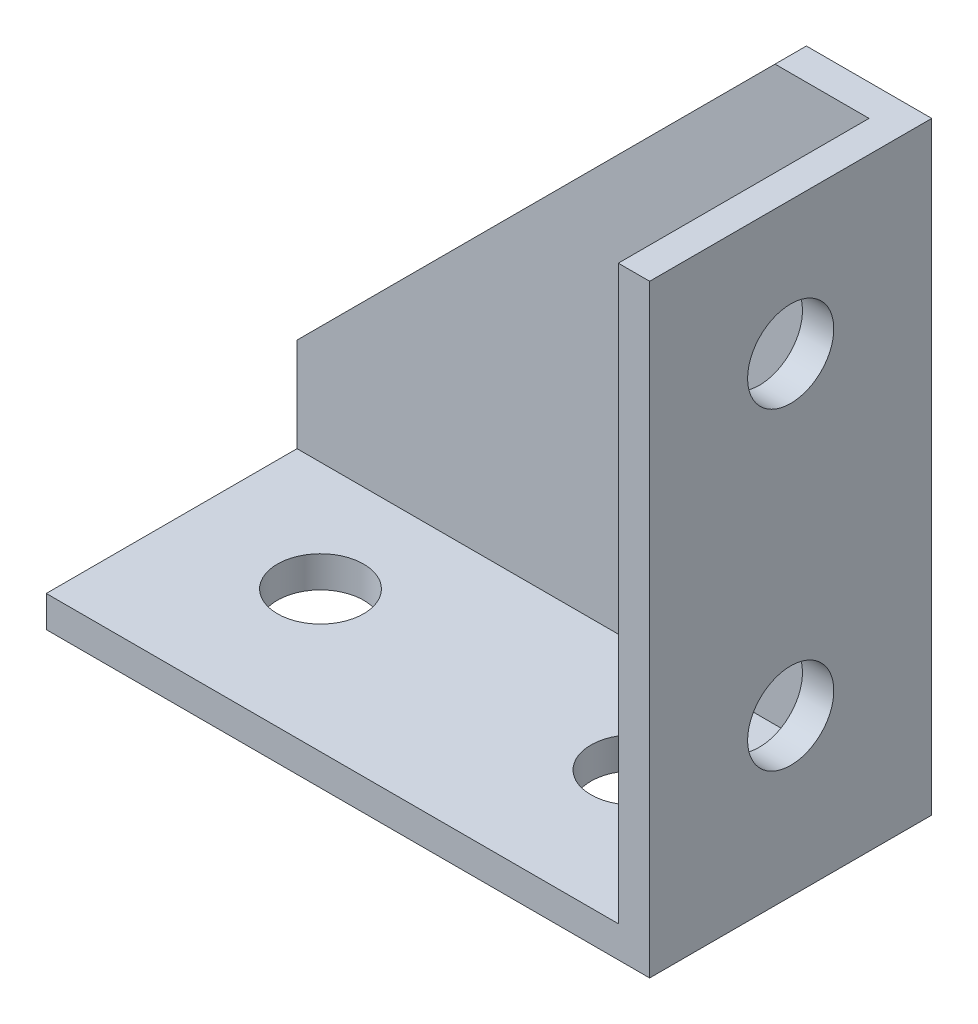
SolidWorks part; units mm, degrees
material "1060 Сплав"
ref_plane "Top" through (0, 0, 0) normal (0, 0, 1) x (1, 0, 0)
ref_plane "Сверху" through (0, 0, 0) normal (0, 1, 0) x (1, 0, 0)
ref_plane "Справа" through (0, 0, 0) normal (1, 0, 0) x (0, 0, -1)
sketch "Эскиз1" plane through (0, 0, 0) normal (0, 0, 1) x (1, 0, 0)
  line L0 (0, 0) -> (0, 8)
  line L1 (0, 8) -> (30.5, 38.5)
  line L2 (30.5, 38.5) -> (38.5, 38.5)
  line L3 (0, 0) -> (38.5, 0)
  line L4 (38.5, 0) -> (38.5, 38.5)
extrude "Бобышка-Вытянуть1" add sketch "Эскиз1" along normal blind 18
sketch "Эскиз2" plane through (0, 0, 18) normal (0, 0, 1) x (1, 0, 0)
  line L0 (0, 2) -> (36.5, 2)
  line L1 (0, 8) -> (0, 0) construction
  line L2 (36.5, 2) -> (36.5, 38.5)
  line L3 (38.5, 38.5) -> (30.5, 38.5) construction
  line L4 (36.5, 38.5) -> (30.5, 38.5)
  line L5 (30.5, 38.5) -> (0, 8)
  line L6 (30.5, 38.5) -> (0, 8) construction
  line L7 (0, 8) -> (0, 2)
extrude "Вырез-Вытянуть1" cut sketch "Эскиз2" against normal blind 16
hole_wizard "Отверстие с зазором M51" positions "Эскиз5" profile "Эскиз4" hole size "M5" standard "DIN" end condition through all
sketch "Эскиз5" plane through (0, 2, 0) normal (0, 1, 0) x (1, 0, 0)
  point P0 (8.5, -9)
  point P2 (28.5, -9)
sketch "Эскиз4" plane through (8.5, 2, 9) normal (1, 0, 0) x (0, 0, 1)
  line L0 (0, 0) -> (0, 2)
  line L1 (0, 2) -> (2.75, 2)
  line L2 (2.75, 2) -> (2.75, 0)
  line L5 (2.75, 0) -> (0, 0)
  line L11 (0, -6.35) -> (0, 107.95) construction
  dimension "Диаметр сквозного отверстия" = 5.5
  dimension "Глубина сквозного отверстия" = 2
hole_wizard "Отверстие с зазором M52" positions "Эскиз7" profile "Эскиз6" hole size "M5" standard "DIN" end condition through all
sketch "Эскиз7" plane through (36.5, 0, 0) normal (-1, 0, 0) x (0, 0, 1)
  point P0 (9, 10)
  point P2 (9, 30)
sketch "Эскиз6" plane through (36.5, 10, 9) normal (0, 1, 0) x (0, 0, 1)
  line L0 (0, 0) -> (0, 2)
  line L1 (0, 2) -> (2.75, 2)
  line L2 (2.75, 2) -> (2.75, 0)
  line L5 (2.75, 0) -> (0, 0)
  line L11 (0, -6.35) -> (0, 107.95) construction
  dimension "Диаметр сквозного отверстия" = 5.5
  dimension "Глубина сквозного отверстия" = 2
